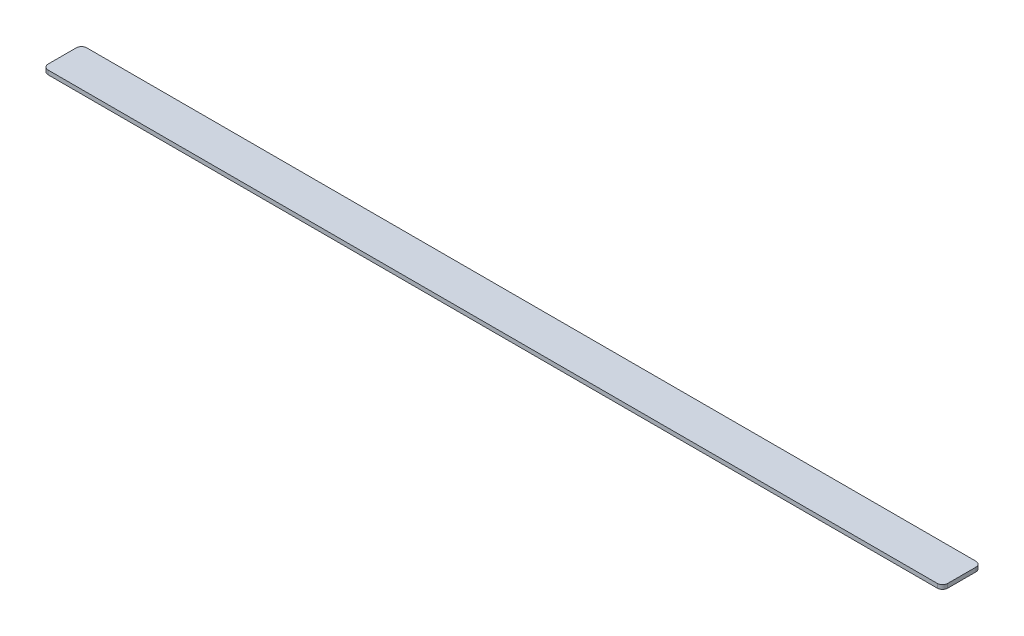
SolidWorks part; units mm, degrees
ref_plane "Front Plane" through (0, 0, 0) normal (0, 0, 1) x (1, 0, 0)
ref_plane "Top Plane" through (0, 0, 0) normal (0, 1, 0) x (1, 0, 0)
ref_plane "Right Plane" through (0, 0, 0) normal (1, 0, 0) x (0, 0, -1)
sketch "Sketch1" plane through (0, 0, 0) normal (0, 1, 0) x (1, 0, 0)
  line L1 (6, 0) -> (1027.5, 0)
  line L2 (0, 6) -> (0, 38.3)
  line L3 (6, 44.3) -> (1027.5, 44.3)
  line L4 (1033.5, 6) -> (1033.5, 38.3)
  arc A0 (6, 44.3) -> (0, 38.3) centre (6, 38.3) ccw
  arc A1 (1027.5, 44.3) -> (1033.5, 38.3) centre (1027.5, 38.3) cw
  arc A2 (0, 6) -> (6, 0) centre (6, 6) ccw
  arc A3 (1033.5, 6) -> (1027.5, 0) centre (1027.5, 6) cw
  dimension "D1" = 6
  dimension "D2" = 6
  dimension "D3" = 6
extrude "Boss-Extrude1" add sketch "Sketch1" along normal blind 4.76
